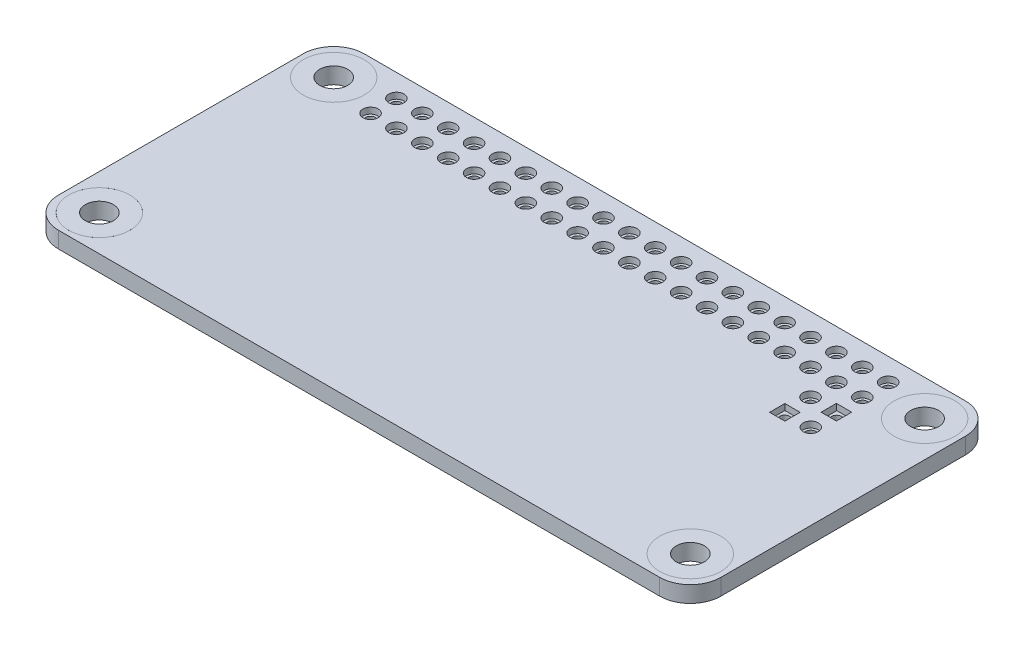
SolidWorks part; units mm, degrees
ref_plane "Front Plane" through (0, 0, 0) normal (0, 0, 1) x (1, 0, 0)
ref_plane "Top Plane" through (0, 0, 0) normal (0, 1, 0) x (1, 0, 0)
ref_plane "Right Plane" through (0, 0, 0) normal (1, 0, 0) x (0, 0, -1)
sketch "Sketch1" plane through (0, 0, 0) normal (0, 1, 0) x (1, 0, 0)
  line L0 (-27.4768, 39.9178) -> (-27.4768, -37.6558) construction
  line L1 (-29.5, -15) -> (29.5, -15)
  line L2 (-32.5, -12) -> (-32.5, 12)
  line L3 (-29.5, 15) -> (29.5, 15)
  line L4 (32.5, -12) -> (32.5, 12)
  line L5 (-32.5, -15) -> (32.5, 15) construction
  line L6 (-32.5, 15) -> (32.5, -15) construction
  line L7 (0, 0) -> (0, 39.9178) construction
  line L9 (-25.5, 14.1112) -> (25.5, 14.1112) construction
  line L10 (-25.5, 14.1112) -> (-25.5, 8.9112) construction
  line L11 (-25.5, 8.9112) -> (25.5, 8.9112) construction
  line L12 (25.5, 14.1112) -> (25.5, 8.9112) construction
  line L13 (23.38, 6.9577) -> (24.88, 6.9577)
  line L14 (23.38, 6.9577) -> (23.38, 8.4577)
  line L15 (23.38, 8.4577) -> (24.88, 8.4577)
  line L16 (24.88, 6.9577) -> (24.88, 8.4577)
  line L17 (23.38, 6.9577) -> (24.88, 8.4577) construction
  line L18 (23.38, 8.4577) -> (24.88, 6.9577) construction
  line L19 (20.8606, 4.4177) -> (22.3606, 4.4177)
  line L20 (20.8606, 4.4177) -> (20.8606, 5.9177)
  line L21 (20.8606, 5.9177) -> (22.3606, 5.9177)
  line L22 (22.3606, 4.4177) -> (22.3606, 5.9177)
  line L23 (20.8606, 4.4177) -> (22.3606, 5.9177) construction
  line L24 (20.8606, 5.9177) -> (22.3606, 4.4177) construction
  arc A0 (-32.5, 12) -> (-29.5, 15) centre (-29.5, 12) cw
  arc A1 (-29.5, -15) -> (-32.5, -12) centre (-29.5, -12) cw
  arc A2 (29.5, -15) -> (32.5, -12) centre (29.5, -12) ccw
  arc A3 (29.5, 15) -> (32.5, 12) centre (29.5, 12) cw
  circle A4 centre (-29, 11.5) radius 3
  circle A5 centre (-29, -11.5) radius 3
  circle A6 centre (29, -11.5) radius 3
  circle A7 centre (-24.13, 12.7877) radius 0.75
  circle A8 centre (-21.59, 12.7877) radius 0.75
  circle A9 centre (-19.05, 12.7877) radius 0.75
  circle A10 centre (-16.51, 12.7877) radius 0.75
  circle A11 centre (-13.97, 12.7877) radius 0.75
  circle A12 centre (-11.43, 12.7877) radius 0.75
  circle A13 centre (-8.89, 12.7877) radius 0.75
  circle A14 centre (-6.35, 12.7877) radius 0.75
  circle A15 centre (-3.81, 12.7877) radius 0.75
  circle A16 centre (-1.27, 12.7877) radius 0.75
  circle A17 centre (1.27, 12.7877) radius 0.75
  circle A18 centre (3.81, 12.7877) radius 0.75
  circle A19 centre (6.35, 12.7877) radius 0.75
  circle A20 centre (8.89, 12.7877) radius 0.75
  circle A21 centre (11.43, 12.7877) radius 0.75
  circle A22 centre (13.97, 12.7877) radius 0.75
  circle A23 centre (16.51, 12.7877) radius 0.75
  circle A24 centre (19.05, 12.7877) radius 0.75
  circle A25 centre (21.59, 12.7877) radius 0.75
  circle A26 centre (24.13, 12.7877) radius 0.75
  circle A27 centre (-21.59, 10.2477) radius 0.75
  circle A28 centre (-19.05, 10.2477) radius 0.75
  circle A29 centre (-16.51, 10.2477) radius 0.75
  circle A30 centre (-13.97, 10.2477) radius 0.75
  circle A31 centre (-11.43, 10.2477) radius 0.75
  circle A32 centre (-8.89, 10.2477) radius 0.75
  circle A33 centre (-6.35, 10.2477) radius 0.75
  circle A34 centre (-3.81, 10.2477) radius 0.75
  circle A35 centre (-1.27, 10.2477) radius 0.75
  circle A36 centre (1.27, 10.2477) radius 0.75
  circle A37 centre (3.81, 10.2477) radius 0.75
  circle A38 centre (6.35, 10.2477) radius 0.75
  circle A39 centre (8.89, 10.2477) radius 0.75
  circle A40 centre (11.43, 10.2477) radius 0.75
  circle A41 centre (13.97, 10.2477) radius 0.75
  circle A42 centre (16.51, 10.2477) radius 0.75
  circle A43 centre (19.05, 10.2477) radius 0.75
  circle A44 centre (21.59, 10.2477) radius 0.75
  circle A45 centre (24.13, 10.2477) radius 0.75
  circle A46 centre (-24.13, 10.2477) radius 0.75
  circle A47 centre (21.59, 7.7077) radius 0.75
  circle A48 centre (24.1506, 5.1677) radius 0.75
  circle A49 centre (29, 11.5) radius 3
  point P0 (0, 0)
  point P32 (0, 8.9112)
  point P117 (24.13, 7.7077)
  point P122 (21.6106, 5.1677)
  dimension "D3" = 3
  dimension "D4" = 51
  dimension "D5" = 6
  dimension "D11" = 1.5
  dimension "D12" = 2
  dimension "D15" = 1.5
  dimension "D16" = 1.5
  dimension "D27" = 6
  dimension "D28" = 6
  dimension "D1" = 65
  dimension "D2" = 30
  dimension "D6" = 23
  dimension "D7" = 29
  dimension "D8" = 3.5
  dimension "D9" = 5.2
  dimension "D10" = 29
  dimension "D13" = 1.27
  dimension "D14" = 20
  dimension "D17" = 2.54
  dimension "D18" = 2.54
  dimension "D19" = 2.54
  dimension "D20" = 2.54
  dimension "D21" = 2.54
  dimension "D22" = 2.54
  dimension "D23" = 1.5
  dimension "D24" = 1.5
  dimension "D25" = 1.5
  dimension "D26" = 1.5
extrude "Boss-Extrude1" add sketch "Sketch1" along normal blind 1.6
sketch "Sketch2" plane through (0, 0, 0) normal (0, 1, 0) x (1, 0, 0)
  circle A0 centre (-24.13, 12.7877) radius 0.75 construction
  circle A1 centre (-24.13, 12.7877) radius 0.75
  circle A3 centre (-24.13, 12.7877) radius 0.5
  dimension "D1" = 1
extrude "Boss-Extrude2" add sketch "Sketch2" along normal blind 1 separate body
pattern_linear "LPattern2" count 20 spacing 2.54 along (1, 0, 0) count 2 spacing 2.54 along (0, 0, 1) of bodies 102
sketch "Sketch3" plane through (0, 0, 0) normal (0, 1, 0) x (1, 0, 0)
  line L1 (20.8194, 4.4177) -> (22.3606, 4.4177)
  line L2 (20.8194, 4.4177) -> (20.8194, 5.9177)
  line L3 (20.8194, 5.9177) -> (22.3606, 5.9177)
  line L4 (22.3606, 4.4177) -> (22.3606, 5.9177)
  line L5 (20.8194, 4.4177) -> (22.3606, 5.9177) construction
  line L6 (20.8194, 5.9177) -> (22.3606, 4.4177) construction
  line L7 (23.4212, 6.9577) -> (24.88, 6.9577)
  line L8 (23.4212, 6.9577) -> (23.4212, 8.4577)
  line L9 (23.4212, 8.4577) -> (24.88, 8.4577)
  line L10 (24.88, 6.9577) -> (24.88, 8.4577)
  line L11 (23.4212, 6.9577) -> (24.88, 8.4577) construction
  line L12 (23.4212, 8.4577) -> (24.88, 6.9577) construction
  circle A0 centre (21.59, 7.7077) radius 0.75
  circle A1 centre (21.59, 7.7077) radius 0.5
  circle A2 centre (24.1506, 5.1677) radius 0.75
  circle A3 centre (24.1506, 5.1677) radius 0.5
  circle A4 centre (24.1506, 7.7077) radius 0.5
  circle A5 centre (21.59, 5.1677) radius 0.5
  dimension "D1" = 1
  dimension "D2" = 1
  dimension "D3" = 1
  dimension "D4" = 1
extrude "Boss-Extrude3" add sketch "Sketch3" along normal blind 1 separate body
sketch "Sketch4" plane through (0, 0, 0) normal (0, 1, 0) x (1, 0, 0)
  circle A0 centre (-29, 11.5) radius 3
  circle A1 centre (-29, 11.5) radius 1.375
  dimension "D1" = 2.75
extrude "Boss-Extrude4" add sketch "Sketch4" along normal blind 1.6 separate body
mirror "Mirror1" about plane through (0, 0, 0) normal (1, 0, 0) of bodies 147
mirror "Mirror2" about plane through (0, 0, 0) normal (0, 0, 1) of bodies 147 148
sketch "Sketch5" plane through (0, 0, 0) normal (0, -1, 0) x (1, 0, 0)
  line L0 (-25.5788, 13.0395) -> (-25.5788, 13.5395) construction
  line L1 (-26.0788, 13.0395) -> (-26.0788, 13.5395)
  line L2 (-25.0788, 13.0395) -> (-25.0788, 13.5395)
  line L3 (-14.6788, 13.0395) -> (-14.6788, 13.5395) construction
  line L4 (-15.1788, 13.0395) -> (-15.1788, 13.5395)
  line L5 (-14.1788, 13.0395) -> (-14.1788, 13.5395)
  line L6 (-14.6788, 8.5395) -> (-14.6788, 9.0395) construction
  line L7 (-15.1788, 8.5395) -> (-15.1788, 9.0395)
  line L8 (-14.1788, 8.5395) -> (-14.1788, 9.0395)
  line L9 (-25.5788, 8.5395) -> (-25.5788, 9.0395) construction
  line L10 (-26.0788, 8.5395) -> (-26.0788, 9.0395)
  line L11 (-25.0788, 8.5395) -> (-25.0788, 9.0395)
  arc A0 (-26.0788, 13.0395) -> (-25.0788, 13.0395) centre (-25.5788, 13.0395) ccw
  arc A1 (-25.0788, 13.5395) -> (-26.0788, 13.5395) centre (-25.5788, 13.5395) ccw
  arc A2 (-15.1788, 13.0395) -> (-14.1788, 13.0395) centre (-14.6788, 13.0395) ccw
  arc A3 (-14.1788, 13.5395) -> (-15.1788, 13.5395) centre (-14.6788, 13.5395) ccw
  arc A4 (-15.1788, 8.5395) -> (-14.1788, 8.5395) centre (-14.6788, 8.5395) ccw
  arc A5 (-14.1788, 9.0395) -> (-15.1788, 9.0395) centre (-14.6788, 9.0395) ccw
  arc A6 (-26.0788, 8.5395) -> (-25.0788, 8.5395) centre (-25.5788, 8.5395) ccw
  arc A7 (-25.0788, 9.0395) -> (-26.0788, 9.0395) centre (-25.5788, 9.0395) ccw
  point P2 (-25.5788, 13.2895)
  point P11 (-14.6788, 13.2895)
  point P18 (-14.6788, 8.7895)
  point P25 (-25.5788, 8.7895)
  dimension "D2" = 0.5
  dimension "D1" = 0.5
  dimension "D3" = 2
extrude "Cut-Extrude1" cut sketch "Sketch5" against normal blind 1
